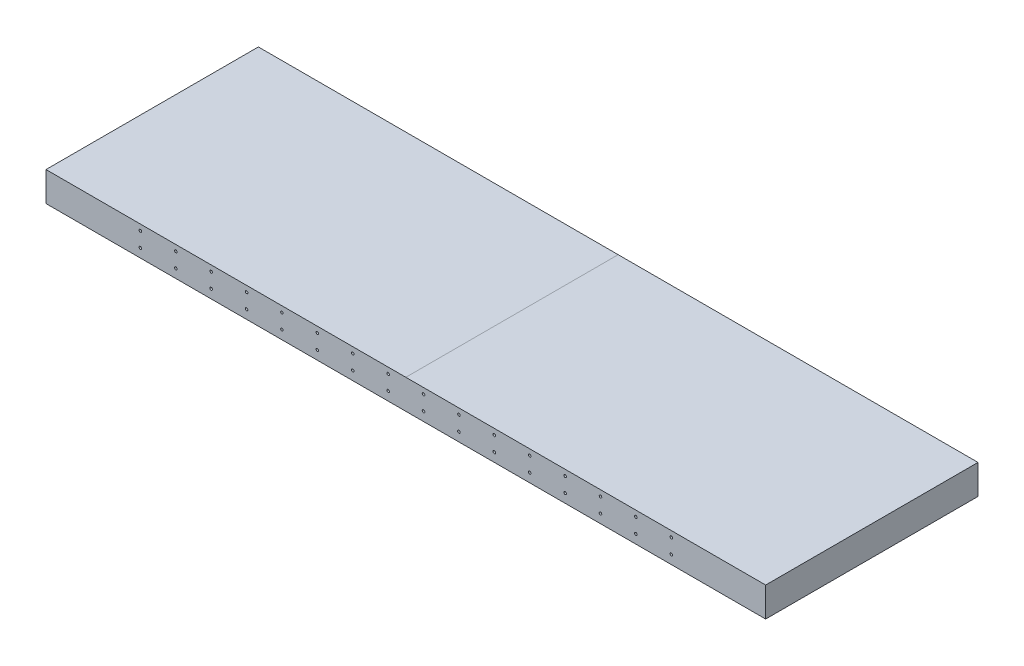
SolidWorks part; units mm, degrees
material "SolidT"
ref_plane "Front Plane" through (0, 0, 0) normal (0, 0, 1) x (1, 0, 0)
ref_plane "Top Plane" through (0, 0, 0) normal (0, 1, 0) x (1, 0, 0)
ref_plane "Right Plane" through (0, 0, 0) normal (1, 0, 0) x (0, 0, -1)
sketch "Sketch1" plane through (0, 0, 0) normal (0, 0, 1) x (1, 0, 0)
  line L1 (0, 0) -> (1549.4, 0)
  line L2 (0, 0) -> (0, 63.5)
  line L3 (0, 63.5) -> (1549.4, 63.5)
  line L4 (1549.4, 0) -> (1549.4, 63.5)
  dimension "D1" = 63.5
  dimension "D2" = 1549.4
extrude "Boss-Extrude1" add sketch "Sketch1" against normal blind 457.2
sketch "Sketch3" plane through (0, 0, -457.2) normal (0, 0, -1) x (-1, 0, 0)
  line L0 (-1549.4, 31.75) -> (0, 31.75) construction
  line L1 (-1549.4, 0) -> (-1549.4, 63.5) construction
  line L2 (0, 63.5) -> (0, 0) construction
  line L3 (-774.7, 63.5) -> (-774.7, 0) construction
  line L4 (-1549.4, 63.5) -> (0, 63.5) construction
  line L5 (0, 0) -> (-1549.4, 0) construction
  line L6 (0, 55.5625) -> (-1549.4, 55.5625) construction
  line L7 (-1549.4, 7.9375) -> (0, 7.9375) construction
  point P16 (-38.1, 55.5625)
  point P17 (-38.1, 7.9375)
  point P19 (-1511.3, 7.9375)
  point P20 (-1511.3, 55.5625)
  dimension "D1" = 23.8125
  dimension "D2" = 23.8125
  dimension "D3" = 38.1
hole_wizard "Hole1" positions "3DSketch1" profile "Sketch4" legacy
sketch3d "3DSketch1"
  point P0 (38.1, 55.5625, -457.2)
  point P3 (38.1, 7.9375, -457.2)
sketch "Sketch4" plane through (38.1, 55.5625, -457.2) normal (1, 0, 0) x (0, 1, 0)
  line L0 (0, 0) -> (0, 5.08)
  line L1 (0, 5.08) -> (2.794, 5.08)
  line L2 (2.794, 5.08) -> (2.794, 0)
  line L3 (2.794, 0) -> (0, 0)
  line L4 (0, 110) -> (0, -10) construction
  dimension "Diameter" = 5.588
  dimension "Depth" = 5.08
pattern_linear "LPattern1" count 4 spacing 25.4 along (1, 0, 0) of "Hole1"
hole_wizard "Hole2" positions "3DSketch2" profile "Sketch5" legacy
sketch3d "3DSketch2"
  point P0 (1511.3, 55.5625, -457.2)
  point P3 (1511.3, 7.9375, -457.2)
sketch "Sketch5" plane through (1511.3, 55.5625, -457.2) normal (1, 0, 0) x (0, 1, 0)
  line L0 (0, 0) -> (0, 5.08)
  line L1 (0, 5.08) -> (2.794, 5.08)
  line L2 (2.794, 5.08) -> (2.794, 0)
  line L3 (2.794, 0) -> (0, 0)
  line L4 (0, 110) -> (0, -10) construction
  dimension "Diameter" = 5.588
  dimension "Depth" = 5.08
pattern_linear "LPattern2" count 4 spacing 25.4 along (-1, 0, 0) of "Hole2"
sketch "Sketch6" plane through (0, 0, 0) normal (0, 0, 1) x (1, 0, 0)
  line L0 (774.7, 63.5) -> (774.7, 0) construction
  line L1 (203.2, 19.05) -> (1346.2, 19.05) construction
  line L2 (0, 0) -> (1549.4, 0) construction
  line L3 (203.2, 50.8) -> (1346.2, 50.8) construction
  point P8 (774.7, 19.05)
  dimension "D1" = 19.05
  dimension "D2" = 1143
  dimension "D3" = 31.75
hole_wizard "Hole3" positions "3DSketch3" profile "Sketch7" legacy
sketch3d "3DSketch3"
  point P0 (203.2, 50.8, 0)
  point P3 (203.2, 19.05, 0)
sketch "Sketch7" plane through (203.2, 50.8, 0) normal (1, 0, 0) x (0, -1, 0)
  line L0 (0, 0) -> (0, 5.08)
  line L1 (0, 5.08) -> (2.794, 5.08)
  line L2 (2.794, 5.08) -> (2.794, 0)
  line L3 (2.794, 0) -> (0, 0)
  line L4 (0, 110) -> (0, -10) construction
  dimension "Diameter" = 5.588
  dimension "Depth" = 5.08
pattern_linear "LPattern3" count 16 spacing 76.2 along (1, 0, 0) of "Hole3"
sketch "Sketch8" plane through (0, 63.5, 0) normal (0, 1, 0) x (1, 0, 0)
  line L1 (0, 457.2) -> (774.7, 457.2)
  line L2 (0, 457.2) -> (0, 0)
  line L3 (0, 0) -> (774.7, 0)
  line L4 (774.7, 457.2) -> (774.7, 0)
split line "Split Line3"
